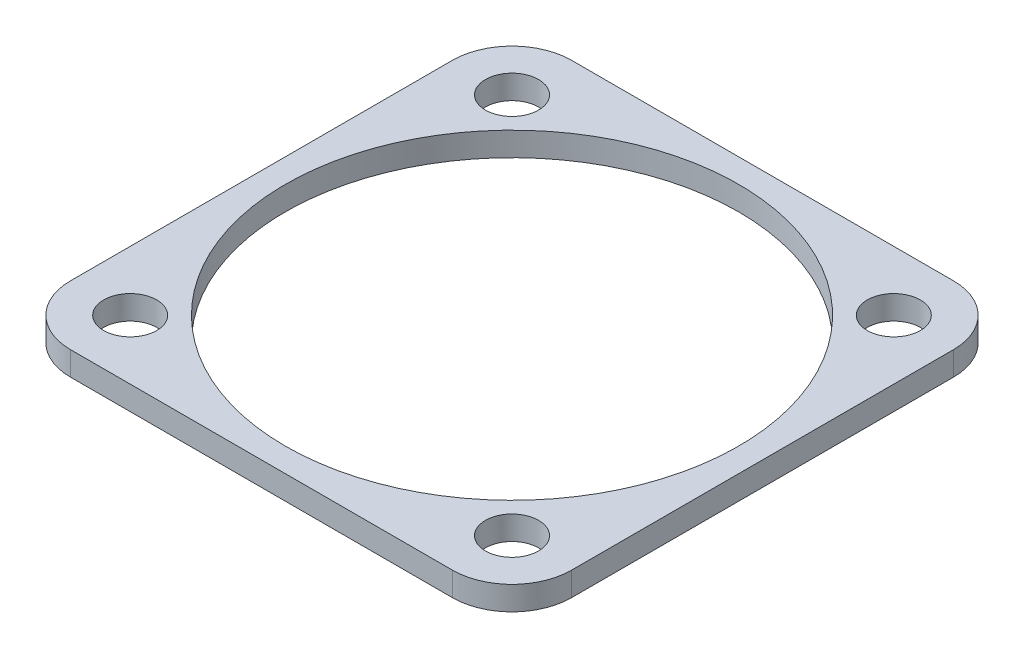
SolidWorks part; units mm, degrees
ref_plane "Front Plane" through (0, 0, 0) normal (0, 0, 1) x (1, 0, 0)
ref_plane "Top Plane" through (0, 0, 0) normal (0, 1, 0) x (1, 0, 0)
ref_plane "Right Plane" through (0, 0, 0) normal (1, 0, 0) x (0, 0, -1)
sketch "Sketch1" plane through (0, 0, 0) normal (0, 1, 0) x (1, 0, 0)
  line L1 (-21, 21) -> (21, 21)
  line L2 (-21, 21) -> (-21, -21)
  line L3 (-21, -21) -> (21, -21)
  line L4 (21, 21) -> (21, -21)
  point P4 (0, 21)
  point P6 (-21, 0)
  dimension "D1" = 42
extrude "Boss-Extrude1" add sketch "Sketch1" along normal blind 2 contours L2 L1 L4 L3
sketch "Sketch2" plane through (0, 2, 0) normal (0, 1, 0) x (1, 0, 0)
  line L0 (-21, 21) -> (-21, -21) construction
  line L1 (-21, 21) -> (21, 21) construction
  line L2 (21, 21) -> (21, -21) construction
  line L3 (-21, -21) -> (21, -21) construction
  circle A0 centre (-16, -16) radius 2.225
  circle A1 centre (-16, 16) radius 2.225
  circle A2 centre (16, 16) radius 2.225
  circle A3 centre (16, -16) radius 2.225
  circle A4 centre (0, 0) radius 19
  dimension "D1" = 4.45
  dimension "D6" = 38
  dimension "D2" = 5
  dimension "D3" = 5
  dimension "D4" = 5
  dimension "D5" = 5
extrude "Cut-Extrude1" cut sketch "Sketch2" against normal up to surface (2 mm away) up to face at (0, 0, 0)
fillet "Fillet1" radius 5 4 edges at (21, 1, -21) (-21, 1, -21) (-21, 1, 21) (21, 1, 21)
